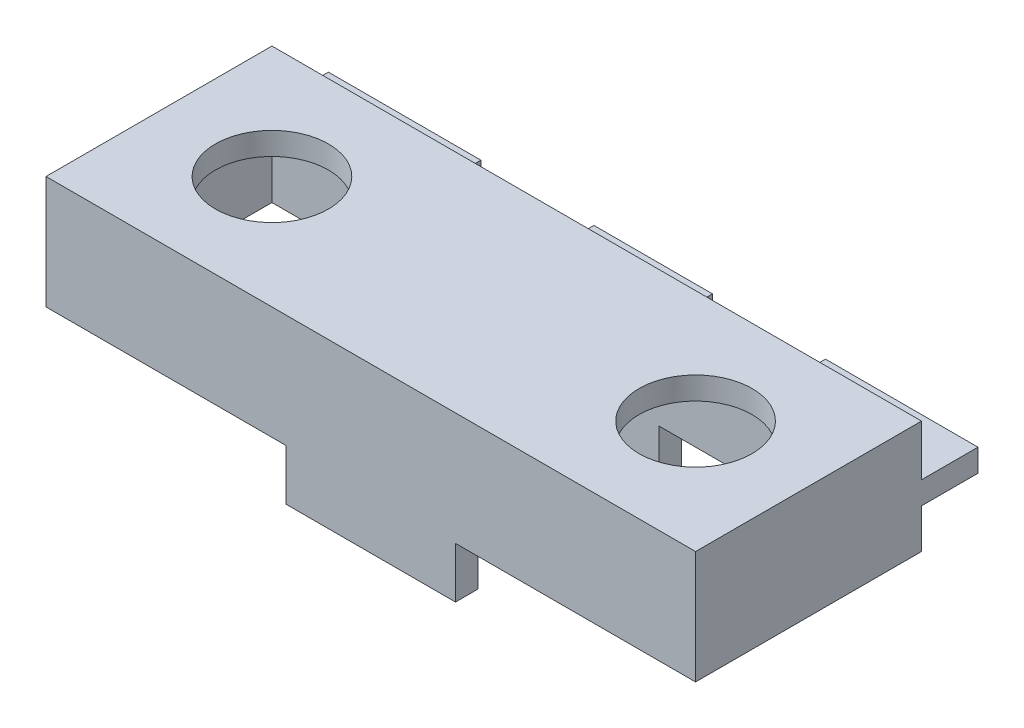
SolidWorks part; units mm, degrees
ref_plane "Front Plane" through (0, 0, 0) normal (0, 0, 1) x (1, 0, 0)
ref_plane "Top Plane" through (0, 0, 0) normal (0, 1, 0) x (1, 0, 0)
ref_plane "Right Plane" through (0, 0, 0) normal (1, 0, 0) x (0, 0, -1)
sketch "Sketch3" plane through (0, 0, 0) normal (0, 1, 0) x (1, 0, 0)
  line L1 (0, 0) -> (146.05, 0)
  line L2 (0, 0) -> (0, 50.8)
  line L3 (0, 50.8) -> (146.05, 50.8)
  line L4 (146.05, 0) -> (146.05, 50.8)
  dimension "D1" = 146.05
  dimension "D2" = 50.8
extrude "Boss-Extrude1" add sketch "Sketch3" against normal blind 25.4
shell "Shell1" thickness 5.08
sketch "Sketch4" plane through (0, 0, 0) normal (0, 1, 0) x (1, 0, 0)
  line L0 (0, 50.8) -> (0, 0) construction
  line L1 (146.05, 0) -> (146.05, 50.8) construction
  line L2 (146.05, 50.8) -> (0, 50.8) construction
  circle A0 centre (25.4, 25.4) radius 12.7
  circle A1 centre (120.65, 25.4) radius 12.7
  dimension "D1" = 25.4
  dimension "D4" = 25.4
  dimension "D2" = 25.4
  dimension "D3" = 25.4
  dimension "D5" = 25.4
  dimension "D6" = 25.4
extrude "Cut-Extrude1" cut sketch "Sketch4" against normal blind 6.35
sketch "Sketch5" plane through (0, -25.4, 0) normal (0, -1, 0) x (1, 0, 0)
  line L0 (73.025, 0) -> (73.025, -50.8) construction
  line L1 (0, 0) -> (146.05, 0) construction
  line L2 (146.05, -50.8) -> (0, -50.8) construction
  line L3 (73.025, 0) -> (92.075, 0)
  line L4 (92.075, 0) -> (92.075, -5.08)
  line L5 (5.08, -5.08) -> (140.97, -5.08) construction
  line L6 (92.075, -5.08) -> (73.025, -5.08)
  line L7 (5.08, -5.08) -> (140.97, -5.08) construction
  line L8 (73.025, -5.08) -> (73.025, 0)
  line L9 (0, -25.4) -> (146.05, -25.4) construction
  line L10 (0, -50.8) -> (0, 0) construction
  line L11 (146.05, 0) -> (146.05, -50.8) construction
  line L12 (140.97, -45.72) -> (5.08, -45.72) construction
  line L13 (73.025, -5.08) -> (53.975, -5.08)
  line L14 (73.025, -5.08) -> (73.025, 0)
  line L15 (73.025, 0) -> (53.975, 0)
  line L16 (53.975, -5.08) -> (53.975, 0)
  line L17 (73.025, -45.72) -> (92.075, -45.72)
  line L18 (73.025, -45.72) -> (73.025, -50.8)
  line L19 (73.025, -50.8) -> (92.075, -50.8)
  line L20 (92.075, -45.72) -> (92.075, -50.8)
  line L22 (73.025, -45.72) -> (53.975, -45.72)
  line L23 (73.025, -45.72) -> (73.025, -50.8)
  line L24 (73.025, -50.8) -> (53.975, -50.8)
  line L25 (53.975, -45.72) -> (53.975, -50.8)
  point P29 (53.975, -50.8)
  dimension "D1" = 19.05
  dimension "D2" = 19.05
  dimension "D3" = 38.1
  dimension "D4" = 19.05
  dimension "D5" = 5.08
extrude "Boss-Extrude2" add sketch "Sketch5" along normal blind 11.43 contours L8 L3 L4 L6 | L14 L13 L16 L15 | L23 L22 L25 L24 | L18 L17 L20 L19
sketch "Sketch6" plane through (0, 0, -50.8) normal (0, 0, -1) x (-1, 0, 0)
  line L0 (-146.05, -25.4) -> (-146.05, 0) construction
  line L1 (-146.05, -11.43) -> (-111.76, -11.43)
  line L2 (-146.05, -11.43) -> (-146.05, -16.51)
  line L3 (-146.05, -16.51) -> (-111.76, -16.51)
  line L4 (-111.76, -11.43) -> (-111.76, -16.51)
  line L5 (0, -25.4) -> (0, 0) construction
  line L6 (-86.36, -11.43) -> (-59.69, -11.43)
  line L7 (-86.36, -11.43) -> (-86.36, -16.51)
  line L8 (-86.36, -16.51) -> (-59.69, -16.51)
  line L9 (-59.69, -11.43) -> (-59.69, -16.51)
  line L10 (-34.29, -11.43) -> (0, -11.43)
  line L11 (-34.29, -11.43) -> (-34.29, -16.51)
  line L12 (-34.29, -16.51) -> (0, -16.51)
  line L13 (0, -11.43) -> (0, -16.51)
  line L15 (-146.05, 0) -> (0, 0) construction
  point P16 (-111.76, -16.0628)
  dimension "D1" = 34.29
  dimension "D2" = 26.67
  dimension "D3" = 25.4
  dimension "D4" = 25.4
  dimension "D5" = 11.43
  dimension "D6" = 5.08
extrude "Boss-Extrude3" add sketch "Sketch6" along normal blind 12.7
